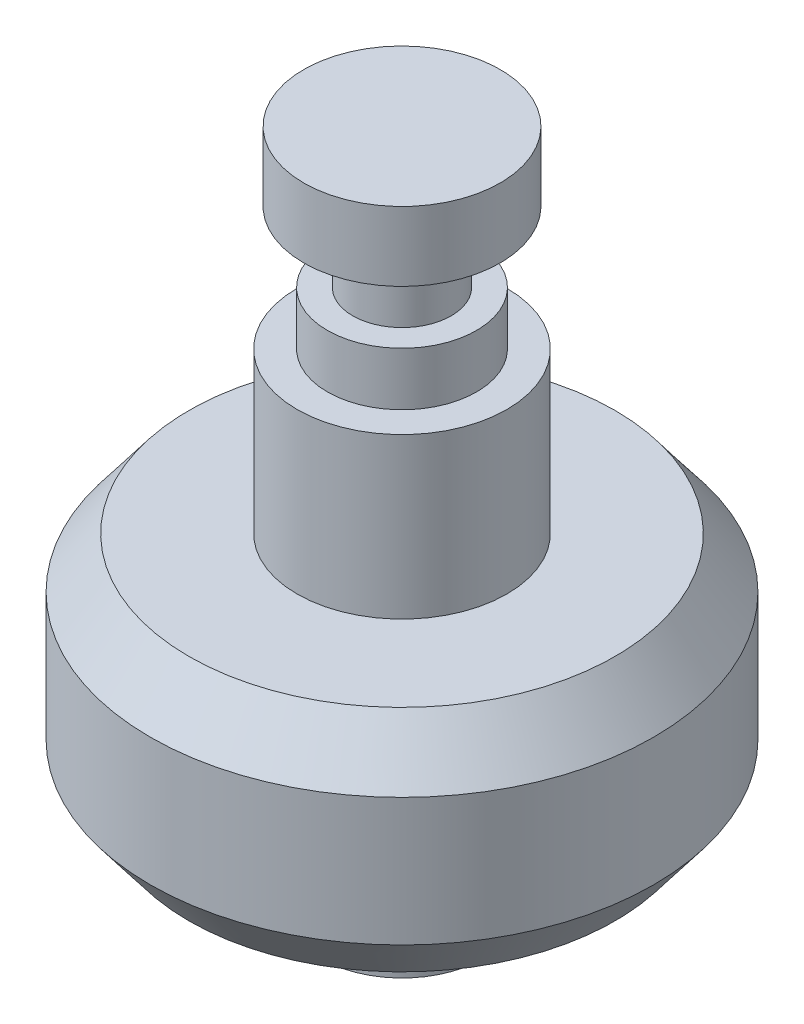
SolidWorks part; units mm, degrees
ref_plane "Front Plane" through (0, 0, 0) normal (0, 0, 1) x (1, 0, 0)
ref_plane "Top Plane" through (0, 0, 0) normal (0, 1, 0) x (1, 0, 0)
ref_plane "Right Plane" through (0, 0, 0) normal (1, 0, 0) x (0, 0, -1)
sketch "Sketch1" plane through (0, 0, 0) normal (1, 0, 0) x (0, 0, -1)
  line L0 (0, 0) -> (0, -32.4358)
  line L1 (0, 0) -> (4.6863, 0)
  line L2 (4.6863, 0) -> (4.6863, -3.302)
  line L3 (2.3495, -3.302) -> (2.3495, -6.6548)
  line L4 (2.3495, -3.302) -> (4.6863, -3.302)
  line L5 (2.3495, -6.6548) -> (3.556, -6.6548)
  line L6 (3.556, -6.6548) -> (3.556, -9.1948)
  line L7 (3.556, -9.1948) -> (5.0038, -9.1948)
  line L8 (5.0038, -9.1948) -> (5.0038, -16.8148)
  line L9 (5.0038, -16.8148) -> (10.16, -16.8148)
  line L10 (10.16, -16.8148) -> (12.0015, -19.2278)
  line L11 (12.0015, -19.2278) -> (12.0015, -25.3238)
  line L12 (12.0015, -25.3238) -> (10.16, -27.7368)
  line L13 (10.16, -27.7368) -> (3.8735, -27.7368)
  line L14 (3.8735, -27.7368) -> (3.8735, -32.4358)
  line L15 (3.8735, -32.4358) -> (0, -32.4358)
  line L16 (10.16, -16.8148) -> (10.16, -27.7368) construction
  line L17 (0, 0) -> (0, -50000) construction
  dimension "D2" = 4.6863
  dimension "D3" = 3.302
  dimension "D4" = 2.3495
  dimension "D5" = 3.3528
  dimension "D6" = 3.556
  dimension "D7" = 2.54
  dimension "D8" = 5.0038
  dimension "D9" = 7.62
  dimension "D10" = 10.16
  dimension "D11" = 3.8735
  dimension "D12" = 4.699
  dimension "D13" = 6.096
  dimension "D14" = 12.0015
  dimension "D15" = 10.922
revolve "Revolve1" add sketch "Sketch1" angle 360 about L17
